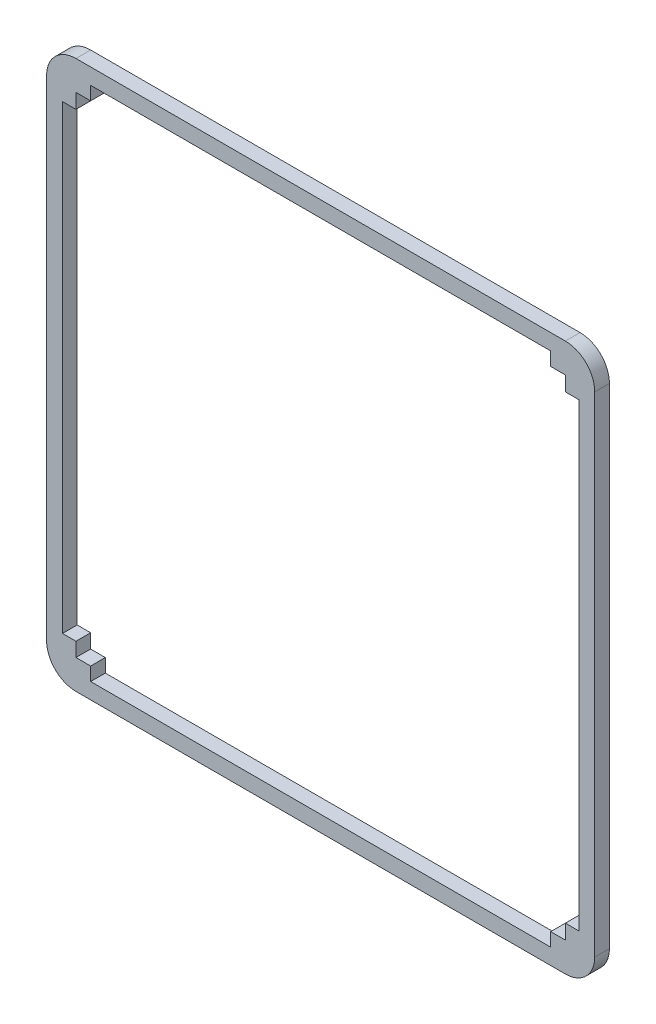
SolidWorks part; units mm, degrees
ref_plane "前视基准面" through (0, 0, 0) normal (0, 0, 1) x (1, 0, 0)
ref_plane "上视基准面" through (0, 0, 0) normal (0, 1, 0) x (1, 0, 0)
ref_plane "右视基准面" through (0, 0, 0) normal (1, 0, 0) x (0, 0, -1)
sketch "草图1" plane through (0, 0, 0) normal (0, 0, 1) x (1, 0, 0)
  line L0 (97, -2.75) -> (3, -2.75)
  line L1 (0, 0) -> (100, 0)
  line L2 (0, 0) -> (0, 100)
  line L3 (0, 100) -> (100, 100)
  line L4 (100, 0) -> (100, 100)
  line L5 (0, 0) -> (100, 0)
  line L7 (0, -6) -> (100, -6)
  line L10 (100, 0) -> (100, 100)
  line L12 (106, 0) -> (106, 100)
  line L13 (0, 100) -> (100, 100)
  line L15 (0, 106) -> (100, 106)
  line L18 (0, 100) -> (0, 0)
  line L20 (-6, 100) -> (-6, 0)
  line L37 (0, 0) -> (100, 0)
  line L41 (0, 0) -> (100, 0)
  line L42 (0, 0) -> (0, 100)
  line L43 (0, 100) -> (100, 100)
  line L44 (100, 0) -> (100, 100)
  line L46 (100, 0) -> (100, 100)
  line L48 (102.75, 3) -> (102.75, 97)
  line L49 (100, 100) -> (0, 100)
  line L51 (97, 102.75) -> (3, 102.75)
  line L54 (0, 100) -> (0, 0)
  line L60 (0, 100) -> (0, 97)
  line L63 (0, 100) -> (3, 100)
  line L64 (3, 102.75) -> (3, 100)
  line L67 (102.75, 97) -> (100, 97)
  line L68 (100, 100) -> (100, 97)
  line L69 (100, 100) -> (97, 100)
  line L72 (97, 100) -> (97, 102.75)
  line L75 (102.75, 3) -> (100, 3)
  line L76 (100, 0) -> (100, 3)
  line L77 (100, 0) -> (97, 0)
  line L80 (97, 0) -> (97, -2.75)
  line L81 (0, 3.0155) -> (0, 97)
  line L82 (0, 0) -> (3, 0)
  line L85 (3, 0) -> (3, -2.75)
  line L87 (0, 0) -> (0, 3.0155)
  line L90 (0, 97) -> (0, 0)
  line L99 (0, 97) -> (0, 17)
  line L102 (0, 3.0155) -> (0, 83.0155)
  line L105 (-2.75, 3.0155) -> (-2.75, 2.8855)
  line L107 (-2.75, 3.0155) -> (-2.75, 97)
  line L108 (-2.75, 97) -> (0, 97)
  line L109 (0, 3.0155) -> (0, 97)
  line L110 (-2.75, 2.8855) -> (0, 2.8855)
  arc A0 (0, -6) -> (-6, 0) centre (0, 0) cw
  arc A1 (-6, 100) -> (0, 106) centre (0, 100) cw
  arc A2 (106, 100) -> (100, 106) centre (100, 100) ccw
  arc A3 (100, -6) -> (106, 0) centre (100, 0) ccw
extrude "凸台-拉伸1" add sketch "草图1" along normal blind 3
